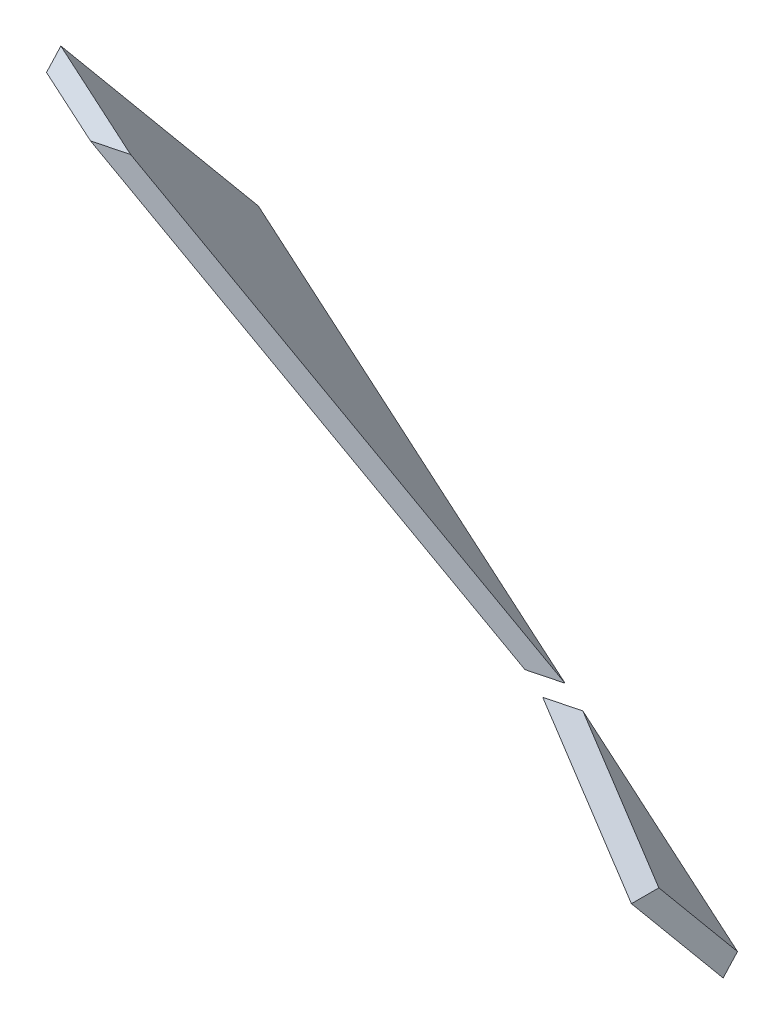
SolidWorks part; units mm, degrees
ref_plane "Front Plane" through (0, 0, 0) normal (0, 0, 1) x (1, 0, 0)
ref_plane "Top Plane" through (0, 0, 0) normal (0, 1, 0) x (1, 0, 0)
ref_plane "Right Plane" through (0, 0, 0) normal (1, 0, 0) x (0, 0, -1)
sketch "Sketch6" plane through (-13.6183, 66.0665, 52.702) normal (-0.1591, 0.7718, 0.6157) x (0.9843, 0.076, 0.1591)
  line L0 (89.0431, 48.9159) -> (88.3582, 52.2389)
  line L1 (89.0431, 48.9159) -> (-40.8497, 86.6509)
  line L2 (88.3582, 52.2389) -> (-41.5346, 89.9739)
  line L3 (-40.8497, 86.6509) -> (-41.5346, 89.9739)
  dimension "D1" = 3
extrude "Boss-Extrude3" add sketch "Sketch6" along normal blind 40
sketch "Sketch7" plane through (-20.2951, 98.4575, 0) normal (-0.2019, 0.9794, 0) x (0.9688, 0.1997, 0.1466)
  line L0 (-12.2359, -131.7406) -> (234.6688, -95.1589)
  line L1 (-12.2359, -131.7406) -> (-29.8233, -13.0364)
  line L2 (234.6688, -95.1589) -> (217.0814, 23.5453)
  line L3 (-29.8233, -13.0364) -> (217.0814, 23.5453)
  line L4 (218.8477, 11.6243) -> (219.5805, 6.6783) construction
  line L6 (217.0814, 23.5453) -> (-29.8233, -13.0364) construction
  line L7 (-16.039, -106.0719) -> (-27.3243, -29.9034) construction
  dimension "D1" = 120
extrude "Cut-Extrude1" cut sketch "Sketch7" along normal through all
